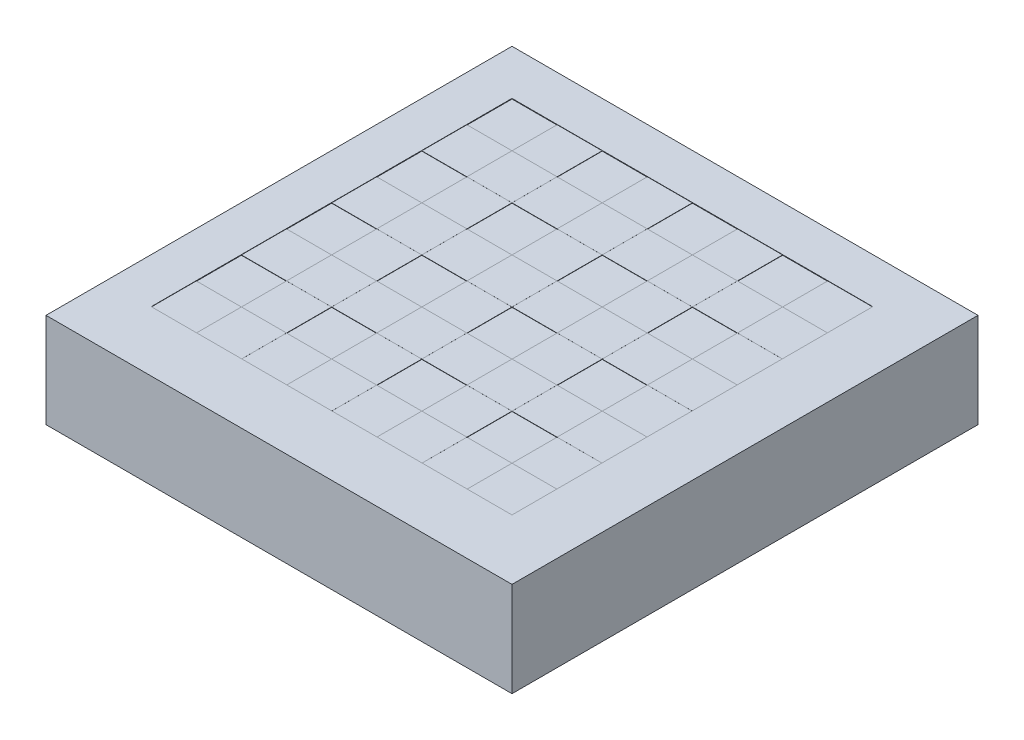
SolidWorks part; units mm, degrees
material "Balsa"
ref_plane "Front Plane" through (0, 0, 0) normal (0, 0, 1) x (1, 0, 0)
ref_plane "Top Plane" through (0, 0, 0) normal (0, 1, 0) x (1, 0, 0)
ref_plane "Right Plane" through (0, 0, 0) normal (1, 0, 0) x (0, 0, -1)
sketch "Sketch1" plane through (0, 0, 0) normal (0, 1, 0) x (1, 0, 0)
  line L1 (0, 0) -> (393.7, 0)
  line L2 (0, 0) -> (0, -393.7)
  line L3 (0, -393.7) -> (393.7, -393.7)
  line L4 (393.7, 0) -> (393.7, -393.7)
  dimension "D1" = 393.7
  dimension "D2" = 393.7
extrude "Boss-Extrude1" add sketch "Sketch1" along normal blind 80
sketch "Esquisse1" plane through (0, 80, 0) normal (0, 1, 0) x (1, 0, 0)
  line L0 (393.7, 0) -> (0, 0) construction
  line L1 (38.1, -38.1) -> (342.9, -38.1)
  line L2 (38.1, -38.1) -> (38.1, -342.9)
  line L3 (38.1, -342.9) -> (342.9, -342.9)
  line L4 (342.9, -38.1) -> (342.9, -342.9)
  line L5 (0, 0) -> (0, -393.7) construction
  dimension "D1" = 304.8
  dimension "D2" = 304.8
  dimension "D3" = 38.1
  dimension "D4" = 38.1
extrude "Enlèv. mat.-Extru.1" cut sketch "Esquisse1" against normal blind 0.254
sketch "Esquisse4" plane through (0, 79.746, 0) normal (0, 1, 0) x (1, 0, 0)
  line L1 (38.1, -38.1) -> (76.2, -38.1)
  line L2 (38.1, -38.1) -> (38.1, -76.2)
  line L3 (38.1, -76.2) -> (76.2, -76.2)
  line L4 (76.2, -38.1) -> (76.2, -76.2)
  dimension "D1" = 38.1
  dimension "D2" = 38.1
extrude "Enlèv. mat.-Extru.2" cut sketch "Esquisse4" against normal blind 0.254
pattern_linear "Répétition linéaire1" count 4 spacing 76.2 along (1, 0, 0) count 4 spacing 76.2 along (0, 0, 1) of "Enlèv. mat.-Extru.2"
sketch "Esquisse5" plane through (0, 79.746, 0) normal (0, 1, 0) x (1, 0, 0)
  line L1 (76.2, -76.2) -> (114.3, -76.2)
  line L2 (76.2, -76.2) -> (76.2, -114.3)
  line L3 (76.2, -114.3) -> (114.3, -114.3)
  line L4 (114.3, -76.2) -> (114.3, -114.3)
extrude "Boss.-Extru.1" add sketch "Esquisse5" along normal blind 0.0254
pattern_linear "Répétition linéaire2" count 4 spacing 76.2 along (0, 0, 1) count 4 spacing 76.2 along (1, 0, 0) of "Boss.-Extru.1"
